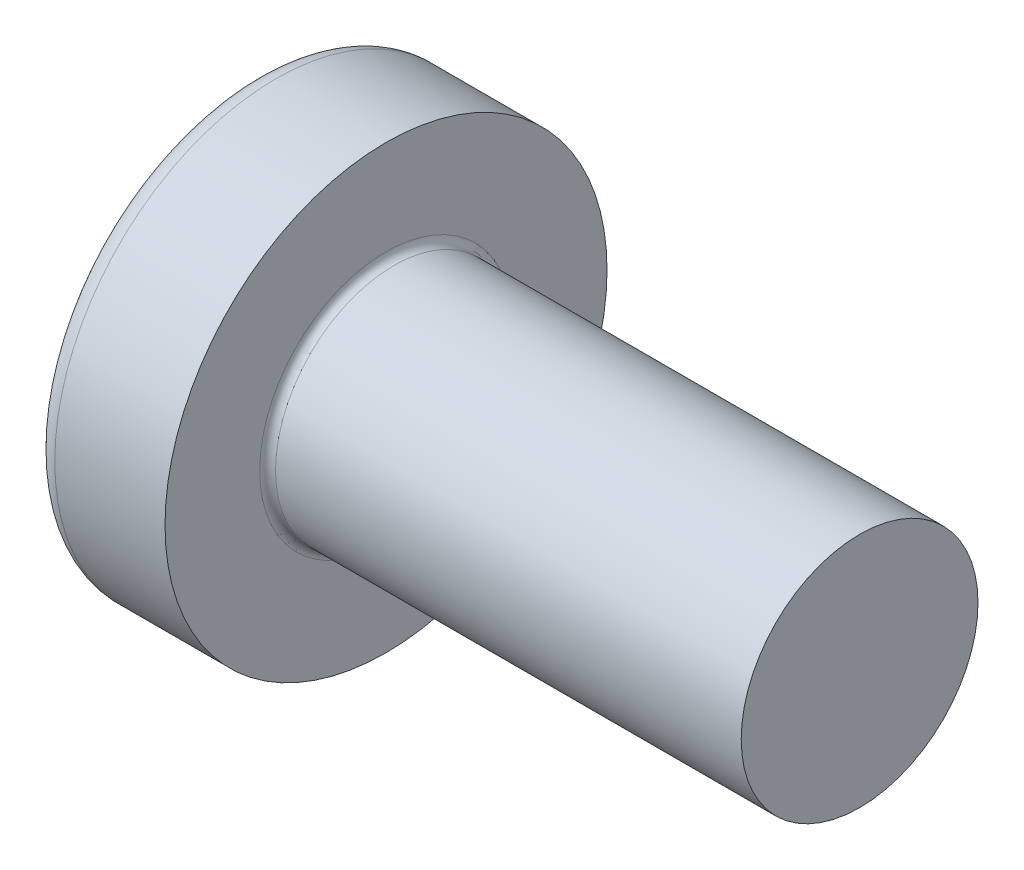
SolidWorks part; units mm, degrees
material "Alliage 7079"
ref_plane "Plane1" through (0, 0, 0) normal (0, 0, 1) x (1, 0, 0)
ref_plane "Plane2" through (0, 0, 0) normal (0, 1, 0) x (1, 0, 0)
ref_plane "Plane3" through (0, 0, 0) normal (1, 0, 0) x (0, 0, -1)
sketch "BodySke" plane through (0, 0, 0) normal (0, 0, 1) x (1, 0, 0)
  line L0 (2.4, 1.5) -> (2.4, 2.8)
  line L1 (2.65, 6.35) -> (2.65, -3.175) construction
  line L2 (-25.4, 0) -> (127, 0) construction
  line L3 (8.4, 0) -> (0, 0)
  line L4 (2.4, 1.5) -> (8.4, 1.5)
  line L5 (8.4, 1.5) -> (8.4, 0)
  line L6 (1.0035, 2.8) -> (2.4, 2.8)
  line L8 (2.4, 6.35) -> (2.4, -3.175) construction
  arc A0 (0.7754, 2.6744) -> (0, 0) centre (5, 0) ccw
  arc A2 (0.7754, 2.6744) -> (1.0035, 2.8) centre (1.0035, 2.53) cw
  dimension "Head_fillet_rad" = 0.27
  dimension "Head_crown_rad" = 5
  dimension "Head_ht" = 2.4
  dimension "Diameter" = 3
  dimension "Length" = 6
  dimension "Head_dia" = 5.6
  dimension "Advance" = 0.5
  dimension "Thread_nom" = 6
revolve "Base-Revolve" add sketch "BodySke"
cosmetic thread "ThreadCosmetic" [suppressed]
fillet "Fillet1" radius 0.1 1 edges at (2.4, 0, 1.5)
sketch "Sketch3" plane through (0, 0, 0) normal (1, 0, 0) x (0, 0, -1)
  line L0 (0.37, -1.4) -> (-0.37, -1.4)
  line L1 (0.37, -1.4) -> (0.37, 1.4)
  line L2 (-0.37, 1.4) -> (0.37, 1.4)
  line L3 (-0.37, 1.4) -> (-0.37, -1.4)
  dimension "D1" = 1.4
  dimension "Cross_dia" = 2.8
  dimension "D2" = 0.37
  dimension "Cross_width" = 0.74
ref_plane "Plane4" through (1.75, 0, 0) normal (1, 0, 0) x (0, 0, -1)
sketch "Sketch4" plane through (1.75, 0, 0) normal (1, 0, 0) x (0, 0, -1)
  line L0 (0.37, -0.5275) -> (-0.37, -0.5275)
  line L1 (0.37, -0.5275) -> (0.37, 0.5275)
  line L2 (-0.37, 0.5275) -> (0.37, 0.5275)
  line L3 (-0.37, 0.5275) -> (-0.37, -0.5275)
  dimension "D1" = 0.74
  dimension "D2" = 1.055
  dimension "D3" = 0.37
  dimension "D4" = 0.5275
loft "Recess" cut profiles "Sketch3", "Sketch4"
pattern_circular "RecPat" count 2 every 90 about axis through (0, 0, 0) along (1, 0, 0) of "Recess"
sketch "RecCorSke" plane through (0, 0, 0) normal (0, 0, 1) x (1, 0, 0)
  line L0 (-3.175, 0) -> (15.875, 0) construction
  line L1 (-25.4, 0) -> (127, 0) construction
  line L2 (0, 0) -> (0, 0.6784)
  line L3 (0, 0.6784) -> (1.75, 0.556)
  line L4 (1.75, 0.556) -> (1.9307, 0)
  line L5 (1.9307, 0) -> (0, 0)
  dimension "Diameter" = 1.112
  dimension "Depth" = 1.75
  dimension "Draft_angle" = 4
  dimension "Bottom_angle" = 18
revolve "RecessCore" cut sketch "RecCorSke" angle 360 about L0
sketch "ThdSchSke" plane through (0, 0, 0) normal (0, 0, 1) x (1, 0, 0)
  line L0 (3.4, -1.2195) -> (3.2036, -1.5)
  line L1 (3.4, -1.2195) -> (3.5964, -1.5)
  line L2 (3.5964, -1.5) -> (3.5964, -1.875)
  line L3 (-3.175, 0) -> (5.1513, 0) construction
  line L5 (3.5964, -1.875) -> (3.2036, -1.875)
  line L6 (3.2036, -1.875) -> (3.2036, -1.5)
  dimension "Thread_minor" = 2.439
  dimension "Diameter" = 3
  dimension "Start" = 3.4
  dimension "SideAngle" = 55
  dimension "VeeAngle" = 70
  dimension "Overcut" = 3.75
revolve "ThreadSchematic" [suppressed] cut sketch "ThdSchSke" angle 360 about L3
pattern_linear "ThdSchPat" [suppressed]
equation "\"D1@Sketch3\" = \"Cross_dia@Sketch3\" / 2"
equation "\"D2@Sketch3\" = \"Cross_width@Sketch3\" / 2"
equation "\"Depth@RecCorSke\" = \"Cross_depth@Plane4\""
equation "\"D1@Sketch4\" = \"Cross_width@Sketch3\""
equation "\"D2@Sketch4\" = \"Cross_dia@Sketch3\" - 2.0 * \"Cross_depth@Plane4\" * tan(26.5  * 0.017453292)"
equation "\"D3@Sketch4\" = \"D1@Sketch4\" / 2"
equation "\"D4@Sketch4\" = \"D2@Sketch4\" / 2"
equation "\"Thread_length@ThreadCosmetic\" = ((sgn( (\"Length@BodySke\" - \"Advance@BodySke\" * 2.0 ) - \"Thread_nom@BodySke\" )-1)*( (\"Length@BodySke\" - \"Advance@BodySke\" * 2.0 ) - \"Thread_nom@BodySke\" ))/-2+ \"Thread_nom@BodySke\""
equation "\"Thread_minor@ThdSchSke\" = \"Thread_minor@ThreadCosmetic\""
equation "\"Diameter@ThdSchSke\" = \"Diameter@BodySke\""
equation "\"Overcut@ThdSchSke\" = \"Diameter@BodySke\" * 1.25"
equation "\"Start@ThdSchSke\" = \"Head_ht@BodySke\" + \"Length@BodySke\" - \"Thread_length@ThreadCosmetic\"  '---Non-countersunk---"
equation "\"Num_threads@ThdSchPat\" = int( \"Thread_length@ThreadCosmetic\" / \"Advance@BodySke\" + 0.999 )  + 1"
equation "\"Advance@ThdSchPat\" = \"Thread_length@ThreadCosmetic\" /  (\"Num_threads@ThdSchPat\" - 1) 'relax it"
